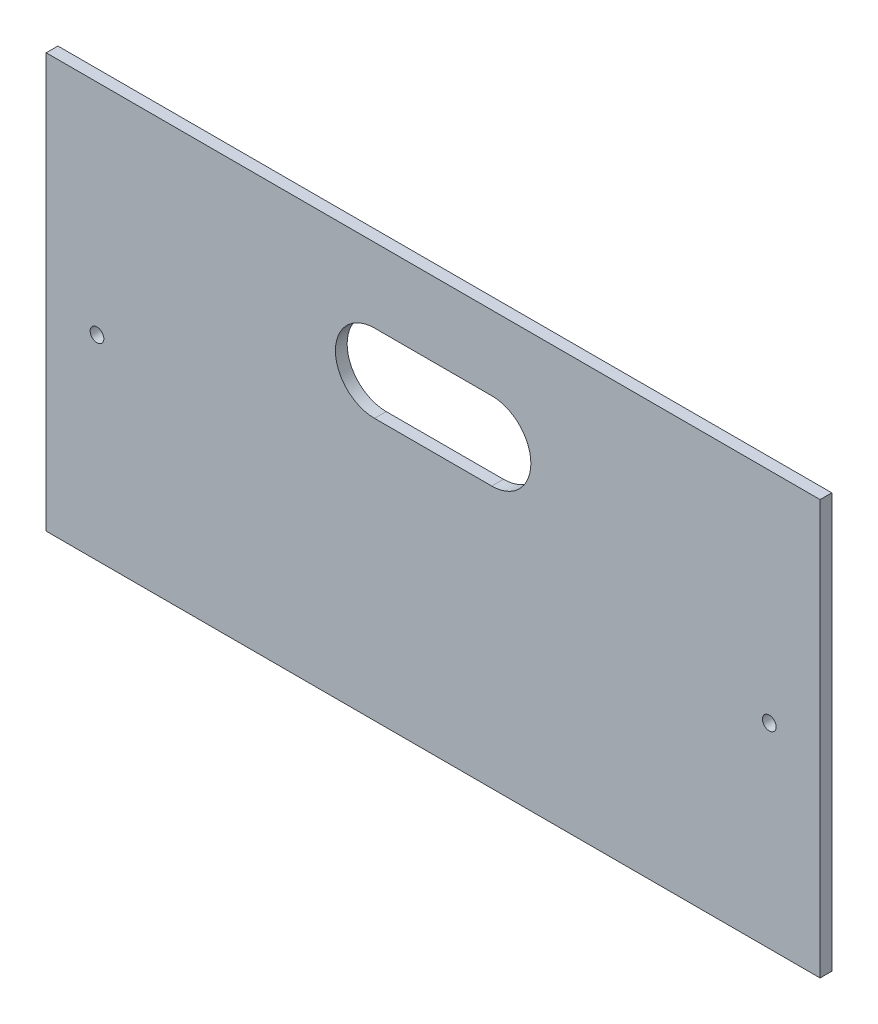
SolidWorks part; units mm, degrees
ref_plane "Plan de face" through (0, 0, 0) normal (0, 0, 1) x (1, 0, 0)
ref_plane "Plan de dessus" through (0, 0, 0) normal (0, 1, 0) x (1, 0, 0)
ref_plane "Plan de droite" through (0, 0, 0) normal (1, 0, 0) x (0, 0, -1)
sketch "Esquisse1" plane through (0, 0, 0) normal (0, 0, 1) x (1, 0, 0)
  line L0 (-99, -3) -> (99, -3) construction
  line L1 (99, 53) -> (-99, 53)
  line L2 (99, 53) -> (99, -53)
  line L3 (99, -53) -> (-99, -53)
  line L4 (-99, 53) -> (-99, -53)
  line L5 (99, 53) -> (-99, -53) construction
  line L6 (99, -53) -> (-99, 53) construction
  line L7 (0, 53) -> (0, -53) construction
  circle A0 centre (-86, -3) radius 1.75
  circle A1 centre (86, -3) radius 1.75
  point P0 (0, 0)
  dimension "D3" = 3.5
  dimension "D1" = 198
  dimension "D2" = 106
  dimension "D4" = 13
  dimension "D5" = 50
extrude "Boss.-Extru.1" add sketch "Esquisse1" along normal blind 3
sketch "Esquisse2" plane through (0, 0, 0) normal (0, 0, -1) x (-1, 0, 0)
  line L0 (-15, 24) -> (15, 24) construction
  line L1 (-15, 34) -> (15, 34)
  line L2 (-15, 14) -> (15, 14)
  line L3 (0, 24) -> (0, 0) construction
  arc A0 (-15, 34) -> (-15, 14) centre (-15, 24) ccw
  arc A1 (15, 14) -> (15, 34) centre (15, 24) ccw
  point P2 (0, 24)
  dimension "D2" = 10
  dimension "D1" = 30
  dimension "D3" = 24
extrude "Enlèv. mat.-Extru.1" cut sketch "Esquisse2" against normal through all
